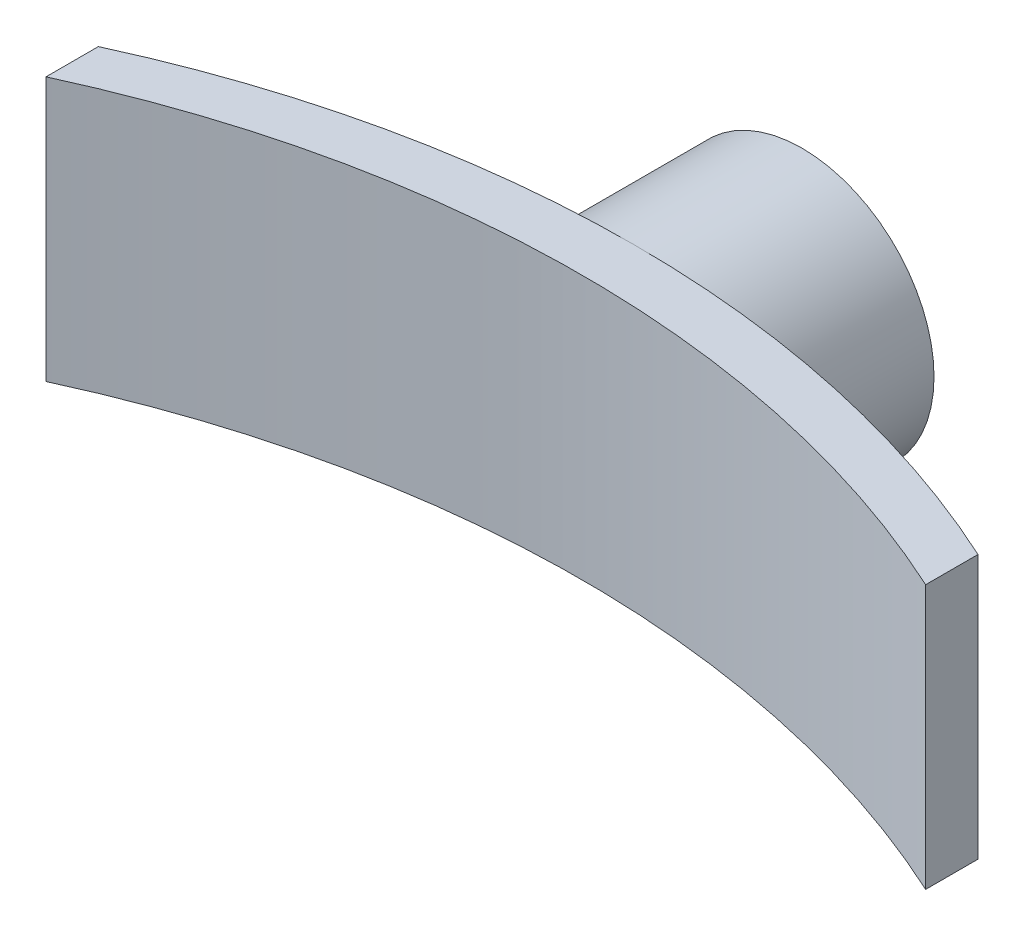
SolidWorks part; units mm, degrees
ref_plane "Front Plane" through (0, 0, 0) normal (0, 0, 1) x (1, 0, 0)
ref_plane "Top Plane" through (0, 0, 0) normal (0, 1, 0) x (1, 0, 0)
ref_plane "Right Plane" through (0, 0, 0) normal (1, 0, 0) x (0, 0, -1)
sketch "Sketch1" plane through (0, 0, 0) normal (0, 0, 1) x (1, 0, 0)
  circle A0 centre (0, 0) radius 2.55
  circle A1 centre (0, 0) radius 15
extrude "Boss-Extrude1" add sketch "Sketch1" along normal blind 20
sketch "Sketch2" plane through (0, 0, 0) normal (0, 1, 0) x (1, 0, 0)
  line L0 (0, -20) -> (0, -30) construction
  line L1 (-15, -20) -> (15, -20) construction
  line L2 (0, -20) -> (0, -15) construction
  line L3 (-50, -30) -> (50, -30) construction
  line L4 (15, -20) -> (0, -20) construction
  line L5 (0, -25) -> (4.7661, -25) construction
  line L6 (50, -35.9495) -> (50, -30)
  line L7 (-50, -35.9495) -> (-50, -30)
  arc A0 (50, -30) -> (-50, -30) centre (0, -138.6854) ccw
  arc A2 (50, -35.9495) -> (-50, -35.9495) centre (0, -144.635) ccw
  point P9 (0, -30)
extrude "Boss-Extrude2" add sketch "Sketch2" along normal through all and the other way through all
